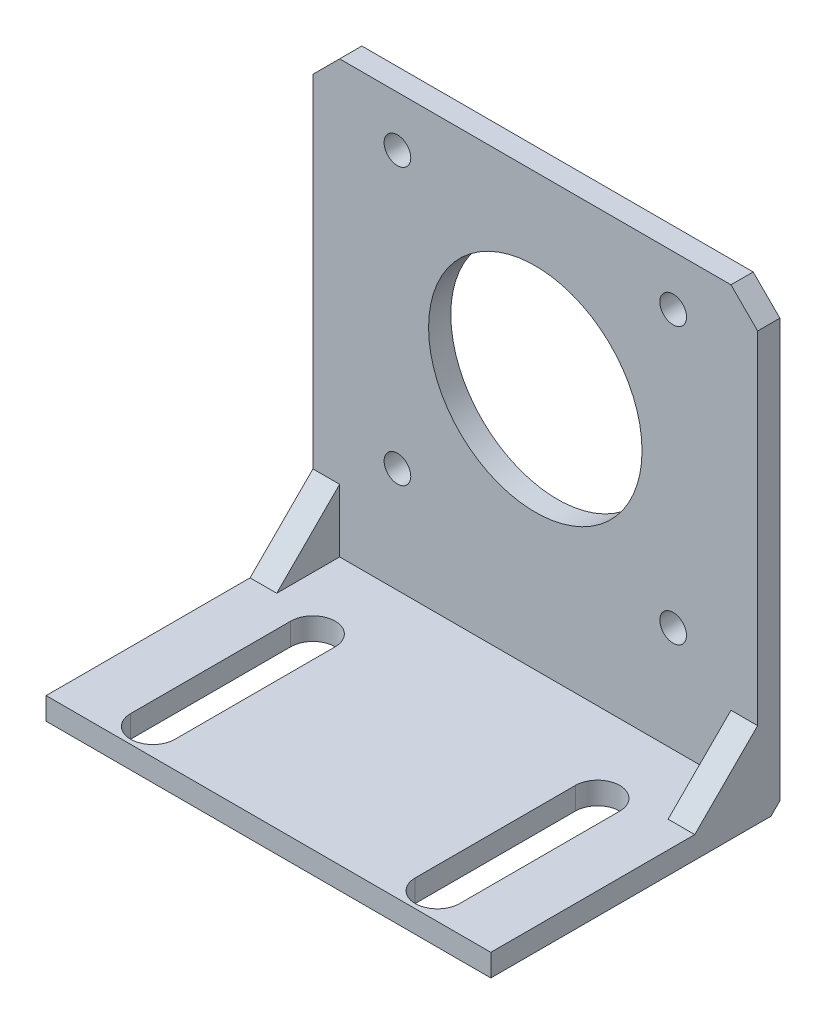
SolidWorks part; units mm, degrees
ref_plane "Front Plane" through (0, 0, 0) normal (0, 0, 1) x (1, 0, 0)
ref_plane "Top Plane" through (0, 0, 0) normal (0, 1, 0) x (1, 0, 0)
ref_plane "Right Plane" through (0, 0, 0) normal (1, 0, 0) x (0, 0, -1)
sketch "Sketch1" plane through (0, 0, 0) normal (0, 0, 1) x (1, 0, 0)
  line L0 (0, 15.6399) -> (0, -15.1371) construction
  line L5 (21.15, 21.15) -> (-21.15, 21.15) construction
  line L6 (21.15, 21.15) -> (21.15, -21.15) construction
  line L7 (21.15, -21.15) -> (-21.15, -21.15) construction
  line L8 (-21.15, 21.15) -> (-21.15, -21.15) construction
  line L9 (21.15, 21.15) -> (-21.15, -21.15) construction
  line L10 (0, -55) -> (0, 55) construction
  line L11 (21.15, -21.15) -> (-21.15, 21.15) construction
  line L12 (13.2145, 0) -> (-16.7833, 0) construction
  line L13 (55, 0) -> (-55, 0) construction
  line L14 (25, 18.15) -> (22, 21.15)
  line L15 (22, 21.15) -> (-22, 21.15)
  line L16 (25, 18.15) -> (25, -23.85)
  line L17 (22, -26.85) -> (-22, -26.85)
  line L18 (-25, 18.15) -> (-25, -23.85)
  line L19 (-22, 21.15) -> (-25, 18.15)
  line L20 (-22, -26.85) -> (-25, -23.85)
  line L21 (25, -23.85) -> (22, -26.85)
  circle A8 centre (0, 0) radius 12
  circle A9 centre (-15.5, 15.5) radius 1.5
  circle A10 centre (15.5, 15.5) radius 1.5
  circle A11 centre (-15.5, -15.5) radius 1.5
  circle A12 centre (15.5, -15.5) radius 1.5
  point P0 (0, 0)
  point P23 (25, 21.15)
  point P24 (-25, -26.85)
  point P25 (25, -26.85)
  point P26 (-25, 21.15)
  point P27 (0, 0)
  dimension "D5" = 15.5
  dimension "D3" = 24
  dimension "D4" = 3
  dimension "D1" = 42.3
  dimension "D2" = 50
  dimension "D6" = 48
extrude "Boss-Extrude1" add sketch "Sketch1" along normal blind 2.5
sketch "Sketch2" plane through (0, 0, 0) normal (0, 0, -1) x (-1, 0, 0)
  line L6 (-25, -23.85) -> (-25, -29.85)
  line L7 (-25, -29.85) -> (25, -29.85)
  line L8 (25, -29.85) -> (25, -23.85)
  line L9 (25, -23.85) -> (22, -26.85)
  line L10 (22, -26.85) -> (-22, -26.85)
  line L11 (-22, -26.85) -> (-25, -23.85)
  dimension "D1" = 3
extrude "Boss-Extrude2" add sketch "Sketch2" against normal blind 2.5
sketch "Sketch3" plane through (0, 0, 2.5) normal (0, 0, 1) x (1, 0, 0)
  line L6 (-25, -29.85) -> (25, -29.85)
  line L7 (-25, -29.85) -> (-25, -27.35)
  line L8 (-25, -27.35) -> (25, -27.35)
  line L9 (25, -29.85) -> (25, -27.35)
  dimension "D1" = 50
  dimension "D2" = 2.5
extrude "Boss-Extrude3" add sketch "Sketch3" along normal blind 30
sketch "Sketch4" plane through (0, -27.35, 0) normal (0, 1, 0) x (1, 0, 0)
  line L0 (0, -29.5) -> (0, -11.5) construction
  line L1 (0, -1.375) -> (0, 1.375) construction
  line L3 (16, -11.5) -> (16, -29.5) construction
  line L4 (-16, -11.5) -> (-16, -29.5) construction
  line L5 (25, -32.5) -> (-25, -32.5) construction
  line L6 (-18.5, -11.5) -> (-13.5, -11.5)
  line L7 (-18.5, -11.5) -> (-18.5, -29.5)
  line L8 (-18.5, -29.5) -> (-13.5, -29.5)
  line L9 (-13.5, -11.5) -> (-13.5, -29.5)
  line L10 (-18.5, -11.5) -> (-13.5, -29.5) construction
  line L11 (-18.5, -29.5) -> (-13.5, -11.5) construction
  line L12 (13.5, -11.5) -> (18.5, -11.5)
  line L13 (13.5, -11.5) -> (13.5, -29.5)
  line L14 (13.5, -29.5) -> (18.5, -29.5)
  line L15 (18.5, -11.5) -> (18.5, -29.5)
  line L16 (13.5, -11.5) -> (18.5, -29.5) construction
  line L17 (13.5, -29.5) -> (18.5, -11.5) construction
  arc A0 (-13.5, -29.5) -> (-18.5, -29.5) centre (-16, -29.5) cw
  arc A1 (13.5, -29.5) -> (18.5, -29.5) centre (16, -29.5) ccw
  arc A2 (18.5, -11.5) -> (13.5, -11.5) centre (16, -11.5) ccw
  arc A3 (-13.5, -11.5) -> (-18.5, -11.5) centre (-16, -11.5) ccw
  point P5 (0, -20.5)
  point P12 (16, -20.5)
  point P13 (-16, -20.5)
  dimension "D1" = 18
  dimension "D2" = 12
  dimension "D3" = 16
  dimension "D4" = 5
extrude "Cut-Extrude1" cut sketch "Sketch4" against normal through all contours L14 A1 | L15 L12 L13 L14 | L12 A2 | L6 A3 | L9 L6 L7 L8 | A0 L8
sketch "Sketch5" plane through (25, 0, 0) normal (1, 0, 0) x (0, 0, -1)
  line L3 (-2.5, -27.35) -> (-2.5, -20.2789)
  line L4 (-2.5, 18.15) -> (-2.5, -27.35) construction
  line L5 (-2.5, -20.2789) -> (-9.5711, -27.35)
  line L6 (-32.5, -27.35) -> (-2.5, -27.35) construction
  line L7 (-9.5711, -27.35) -> (-2.5, -27.35)
  dimension "D1" = 10
  dimension "D2" = 45
extrude "Boss-Extrude4" add sketch "Sketch5" against normal blind 3
mirror "Mirror1" about plane through (0, 0, 0) normal (1, 0, 0) of "Boss-Extrude4"
chamfer "Chamfer1" distance 1 angle 45 1 edges at (0, -29.85, 0)
